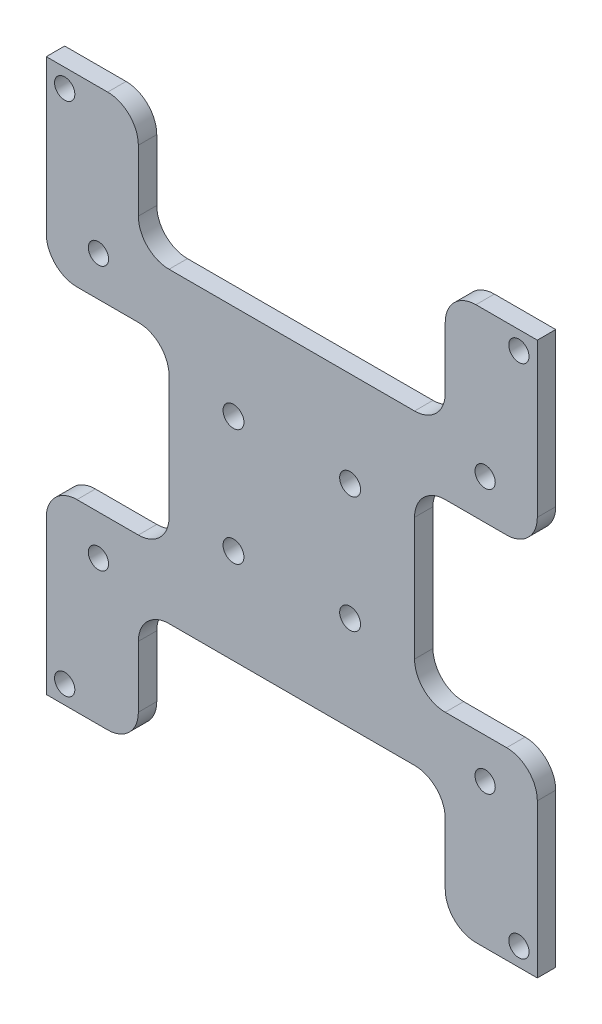
SolidWorks part; units mm, degrees
ref_plane "前视基准面" through (0, 0, 0) normal (0, 0, 1) x (1, 0, 0)
ref_plane "上视基准面" through (0, 0, 0) normal (0, 1, 0) x (1, 0, 0)
ref_plane "右视基准面" through (0, 0, 0) normal (1, 0, 0) x (0, 0, -1)
sketch "草图1" plane through (0, 0, 0) normal (0, 0, 1) x (1, 0, 0)
  line L1 (45.8501, -42.0386) -> (-34.1499, -42.0386)
  line L2 (45.8501, -42.0386) -> (45.8501, 47.9614)
  line L3 (45.8501, 47.9614) -> (-34.1499, 47.9614)
  line L4 (-34.1499, -42.0386) -> (-34.1499, 47.9614)
  dimension "D1" = 80
  dimension "D2" = 90
extrude "凸台-拉伸1" add sketch "草图1" along normal blind 3
sketch "草图2" plane through (0, 0, 0) normal (0, 0, -1) x (-1, 0, 0)
  line L0 (-45.8501, 47.9614) -> (34.1499, 47.9614) construction
  line L1 (-42.8501, 44.9614) -> (31.1499, 44.9614) construction
  line L2 (-42.8501, 44.9614) -> (-42.8501, -39.0386) construction
  line L3 (-42.8501, -39.0386) -> (31.1499, -39.0386) construction
  line L4 (31.1499, 44.9614) -> (31.1499, -39.0386) construction
  line L6 (-45.8501, -42.0386) -> (-45.8501, 47.9614) construction
  circle A0 centre (31.1499, -39.0386) radius 1.65
  circle A1 centre (-42.8501, -39.0386) radius 1.65
  circle A2 centre (31.1499, 44.9614) radius 1.65
  circle A3 centre (-42.8501, 44.9614) radius 1.65
  dimension "D3" = 3.3
  dimension "D4" = 3.3
  dimension "D5" = 3.3
  dimension "D6" = 3.3
  dimension "D1" = 84
  dimension "D2" = 74
  dimension "D7" = 3
  dimension "D8" = 3
extrude "切除-拉伸1" cut sketch "草图2" against normal blind 3
sketch "草图3" plane through (0, 0, 0) normal (0, 0, -1) x (-1, 0, 0)
  line L0 (-45.8501, 47.9614) -> (34.1499, 47.9614) construction
  line L1 (-40.8501, 27.9614) -> (29.1499, 27.9614) construction
  line L2 (-40.8501, 27.9614) -> (-40.8501, -22.0386) construction
  line L3 (-40.8501, -22.0386) -> (29.1499, -22.0386) construction
  line L4 (29.1499, 27.9614) -> (29.1499, -22.0386) construction
  line L6 (34.1499, 47.9614) -> (34.1499, -42.0386) construction
  line L7 (25.6499, -18.5386) -> (-37.3501, -18.5386) construction
  line L8 (-40.8501, 2.9614) -> (29.1499, 2.9614) construction
  line L9 (-5.8501, 27.9614) -> (-5.8501, -22.0386) construction
  line L10 (-30.8501, 47.9614) -> (-30.8501, 27.9614)
  line L11 (-30.8501, 27.9614) -> (19.1499, 27.9614)
  line L12 (19.1499, 27.9614) -> (19.1499, 47.9614)
  line L13 (19.1499, 47.9614) -> (-30.8501, 47.9614)
  line L14 (19.1499, -22.0386) -> (19.1499, -42.0386)
  line L15 (-30.8501, -22.0386) -> (19.1499, -22.0386)
  line L16 (-30.8501, -42.0386) -> (-30.8501, -22.0386)
  line L17 (19.1499, -42.0386) -> (-30.8501, -42.0386)
  line L18 (34.1499, 17.9614) -> (34.1499, -12.0386)
  line L19 (34.1499, -12.0386) -> (14.1499, -12.0386)
  line L20 (14.1499, -12.0386) -> (14.1499, 17.9614)
  line L21 (14.1499, 17.9614) -> (34.1499, 17.9614)
  line L22 (-45.8501, -12.0386) -> (-25.8501, -12.0386)
  line L23 (-25.8501, -12.0386) -> (-25.8501, 17.9614)
  line L24 (-25.8501, 17.9614) -> (-45.8501, 17.9614)
  line L25 (-45.8501, 17.9614) -> (-45.8501, -12.0386)
  line L26 (25.6499, -18.5386) -> (25.6499, 24.4614) construction
  line L27 (25.6499, 24.4614) -> (-37.3501, 24.4614) construction
  line L28 (-37.3501, -18.5386) -> (-37.3501, 24.4614) construction
  line L29 (25.6499, -18.5386) -> (-37.3501, 24.4614) construction
  line L30 (25.6499, 24.4614) -> (-37.3501, -18.5386) construction
  circle A0 centre (-37.3501, 24.4614) radius 1.65
  circle A1 centre (25.6499, 24.4614) radius 1.65
  circle A2 centre (25.6499, -18.5386) radius 1.65
  circle A3 centre (-37.3501, -18.5386) radius 1.65
  point P31 (34.1499, 2.9614)
  point P39 (-5.8501, 2.9614)
  dimension "D7" = 3.3
  dimension "D10" = 3.3
  dimension "D13" = 3.3
  dimension "D14" = 3.3
  dimension "D1" = 50
  dimension "D2" = 70
  dimension "D3" = 20
  dimension "D4" = 5
  dimension "D5" = 63
  dimension "D6" = 43
  dimension "D17" = 50
  dimension "D18" = 50
  dimension "D19" = 15
  dimension "D20" = 15
  dimension "D21" = 20
  dimension "D22" = 30
  dimension "D23" = 30
extrude "切除-拉伸2" cut sketch "草图3" against normal up to next
fillet "圆角1" radius 5 16 edges at (-14.1499, -12.0386, 1.5) (-34.1499, -12.0386, 1.5) (-19.1499, -42.0386, 1.5) (-19.1499, -22.0386, 1.5) (30.8501, -22.0386, 1.5) (30.8501, -42.0386, 1.5) (45.8501, -12.0386, 1.5) (25.8501, -12.0386, 1.5) (-14.1499, 17.9614, 1.5) (25.8501, 17.9614, 1.5) (45.8501, 17.9614, 1.5) (-19.1499, 47.9614, 1.5) (30.8501, 47.9614, 1.5) (30.8501, 27.9614, 1.5) (-19.1499, 27.9614, 1.5) (-34.1499, 17.9614, 1.5)
sketch "草图4" plane through (0, 0, 0) normal (0, 0, -1) x (-1, 0, 0)
  line L0 (14.1499, 12.9614) -> (14.1499, -7.0386) construction
  line L1 (-15.3501, 12.4614) -> (3.6499, 12.4614) construction
  line L2 (-15.3501, 12.4614) -> (-15.3501, -6.5386) construction
  line L3 (-15.3501, -6.5386) -> (3.6499, -6.5386) construction
  line L4 (3.6499, 12.4614) -> (3.6499, -6.5386) construction
  line L5 (-25.8501, 27.9614) -> (14.1499, 27.9614) construction
  circle A0 centre (3.6499, 12.4614) radius 1.7
  circle A1 centre (3.6499, -6.5386) radius 1.7
  circle A2 centre (-15.3501, -6.5386) radius 1.7
  circle A3 centre (-15.3501, 12.4614) radius 1.7
  dimension "D5" = 3.4
  dimension "D6" = 3.4
  dimension "D7" = 3.4
  dimension "D8" = 3.4
  dimension "D1" = 19
  dimension "D2" = 19
  dimension "D3" = 10.5
  dimension "D4" = 15.5
extrude "切除-拉伸3" cut sketch "草图4" against normal up to next
